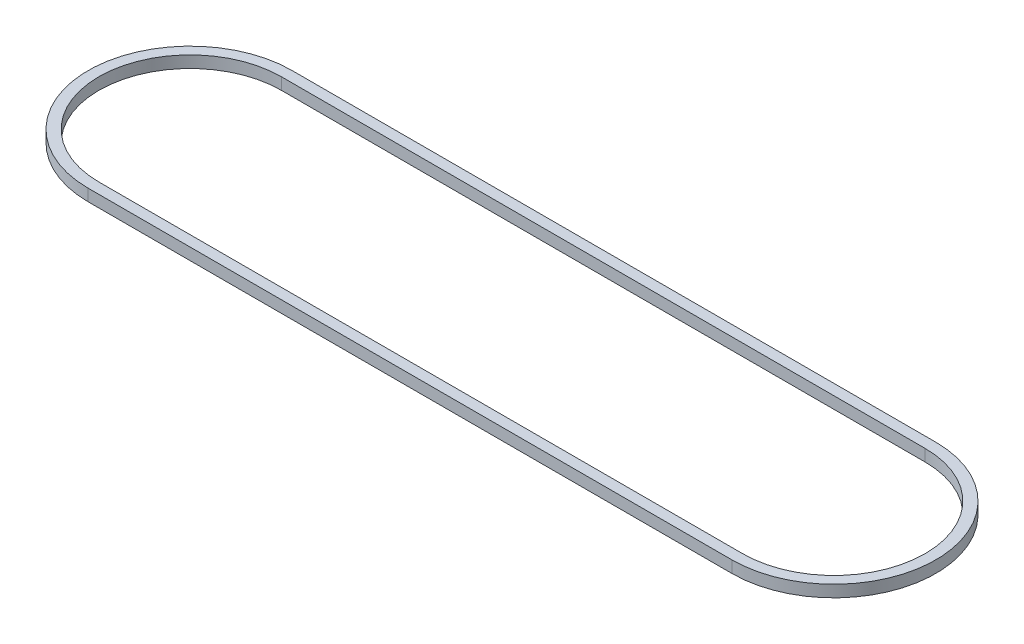
SolidWorks part; units mm, degrees
ref_plane "Front Plane" through (0, 0, 0) normal (0, 0, 1) x (1, 0, 0)
ref_plane "Top Plane" through (0, 0, 0) normal (0, 1, 0) x (1, 0, 0)
ref_plane "Right Plane" through (0, 0, 0) normal (1, 0, 0) x (0, 0, -1)
sketch "Sketch2" plane through (0, 0, 0) normal (0, 1, 0) x (1, 0, 0)
  line L1 (3000, 950) -> (-3000, 950)
  line L3 (3000, -950) -> (-3000, -950)
  line L5 (3000, 950) -> (-3000, -950) construction
  line L6 (3000, -950) -> (-3000, 950) construction
  arc A0 (-3000, 950) -> (-3000, -950) centre (-3000, 0) ccw
  arc A1 (3000, -950) -> (3000, 950) centre (3000, 0) ccw
  point P0 (0, 0)
  dimension "D1" = 6000
  dimension "D2" = 1900
extrude "Boss-Extrude1" add sketch "Sketch2" along normal blind 110
shell "Shell1" thickness 100
sketch "Sketch5" plane through (0, 100, 0) normal (0, 1, 0) x (1, 0, 0)
  line L0 (-3000, 850) -> (3000, 850)
  line L1 (3000, -850) -> (-3000, -850)
  arc A0 (3000, -850) -> (3000, 850) centre (3000, 0) ccw construction
  arc A1 (-3000, 850) -> (-3000, -850) centre (-3000, 0) ccw
  arc A2 (3000, -850) -> (3000, 850) centre (3000, 0) ccw
extrude "Cut-Extrude1" cut sketch "Sketch5" against normal blind 110
